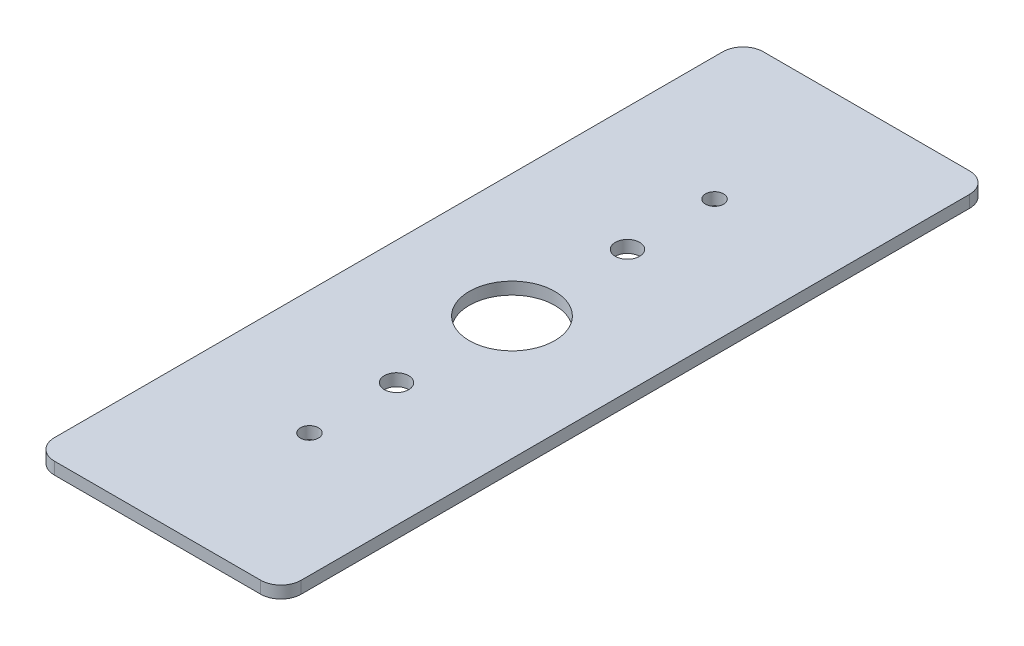
SolidWorks part; units mm, degrees
material "Acrylic (Medium-high impact)"
ref_plane "Front Plane" through (0, 0, 0) normal (0, 0, 1) x (1, 0, 0)
ref_plane "Top Plane" through (0, 0, 0) normal (0, 1, 0) x (1, 0, 0)
ref_plane "Right Plane" through (0, 0, 0) normal (1, 0, 0) x (0, 0, -1)
sketch "Sketch1" plane through (0, 0, 0) normal (0, 1, 0) x (1, 0, 0)
  line L0 (-15.4781, -44.45) -> (-15.4781, 44.45)
  line L1 (15.4781, 44.45) -> (15.4781, -44.45)
  line L2 (-15.4781, 0) -> (15.4781, 0) construction
  line L3 (0, 41.275) -> (0, -41.275) construction
  line L4 (-15.4781, 44.45) -> (15.4781, 44.45)
  line L5 (-15.4781, -44.45) -> (15.4781, -44.45)
  dimension "D2" = 30.9562
  dimension "D1" = 88.9
extrude "Boss-Extrude1" add sketch "Sketch1" along normal blind 1.524
fillet "Fillet1" radius 2.54 4 edges at (15.4781, 0.762, -44.45) (-15.4781, 0.762, -44.45) (15.4781, 0.762, 44.45) (-15.4781, 0.762, 44.45)
sketch "Sketch6" plane through (0, 0, 0) normal (0, -1, 0) x (1, 0, 0)
  line L0 (0, 0) -> (-28.2073, 0) construction
  line L1 (-12.9381, 44.45) -> (12.9381, 44.45) construction
  circle A0 centre (0, 14.478) radius 1.524
  circle A1 centre (0, -14.478) radius 1.524
  point P9 (0, 44.45)
  dimension "D1" = 3.048
  dimension "D2" = 14.478
extrude "Cut-Extrude1" cut sketch "Sketch6" against normal through all
hole_wizard "#4-40 Tapped Hole1" positions "Sketch5" profile "Sketch4" tap size "#4-40" standard "Ansi Inch" end condition through all
sketch "Sketch5" plane through (0, 1.524, 0) normal (0, 1, 0) x (-1, 0, 0)
  line L0 (0, 0) -> (16.1552, 0) construction
  point P0 (0, 25.4)
  point P9 (0, -25.4)
  dimension "D1" = 50.8
sketch "Sketch4" plane through (0, 1.524, 25.4) normal (1, 0, 0) x (0, 0, 1)
  line L0 (0, 0) -> (0, 1.524)
  line L1 (0, 1.524) -> (1.1303, 1.524)
  line L2 (1.1303, 1.524) -> (1.1303, 0)
  line L5 (1.1303, 0) -> (0, 0)
  line L11 (0, -6.35) -> (0, 107.95) construction
  dimension "Thread Major Dia." = 2.2606
  dimension "Thru Tap Drill Depth" = 1.524
hole_wizard "1/2-13 Tapped Hole1" positions "Sketch8" profile "Sketch7" tap size "1/2-13" standard "Ansi Inch" end condition through all
sketch "Sketch8" plane through (0, 1.524, 0) normal (0, 1, 0) x (-1, 0, 0)
  point P1 (0, 0)
sketch "Sketch7" plane through (0, 1.524, 0) normal (1, 0, 0) x (0, 0, 1)
  line L0 (0, 0) -> (0, 1.524)
  line L1 (0, 1.524) -> (5.3581, 1.524)
  line L2 (5.3581, 1.524) -> (5.3581, 0)
  line L5 (5.3581, 0) -> (0, 0)
  line L11 (0, -6.35) -> (0, 107.95) construction
  dimension "Thru Tap Drill Dia." = 10.7163
  dimension "Thru Tap Drill Depth" = 1.524
cosmetic thread "Hole Thread1" parameters "D2"=12.7
